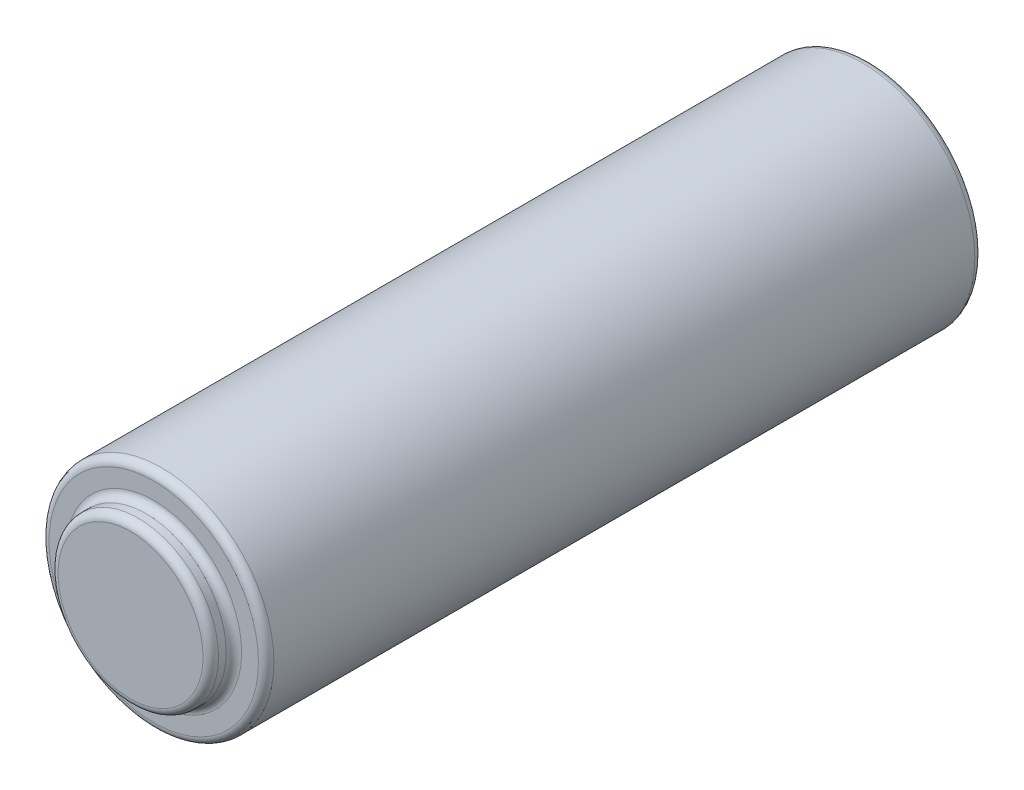
SolidWorks part; units mm, degrees
ref_plane "Front Plane" through (0, 0, 0) normal (0, 0, 1) x (1, 0, 0)
ref_plane "Top Plane" through (0, 0, 0) normal (0, 1, 0) x (1, 0, 0)
ref_plane "Right Plane" through (0, 0, 0) normal (1, 0, 0) x (0, 0, -1)
sketch "Sketch1" plane through (0, 0, 0) normal (0, 0, 1) x (1, 0, 0)
  circle A0 centre (23.495, 8.89) radius 7.4004
  dimension "D1" = 14.8009
extrude "Boss-Extrude1" add sketch "Sketch1" along normal blind 47.1575
sketch "Sketch2" plane through (0, 0, 47.1575) normal (0, 0, 1) x (1, 0, 0)
  circle A0 centre (23.495, 8.89) radius 5.2797
  circle A1 centre (23.495, 8.89) radius 7.4004 construction
extrude "Boss-Extrude2" add sketch "Sketch2" along normal blind 1.524
fillet "Fillet1" radius 0.508 1 edges at (28.7747, 8.89, 48.6815)
fillet "Fillet2" radius 0.508 2 edges at (30.8954, 8.89, 47.1575) (28.7747, 8.89, 47.1575)
fillet "Fillet3" radius 0.508 1 edges at (30.8954, 8.89, 0)
